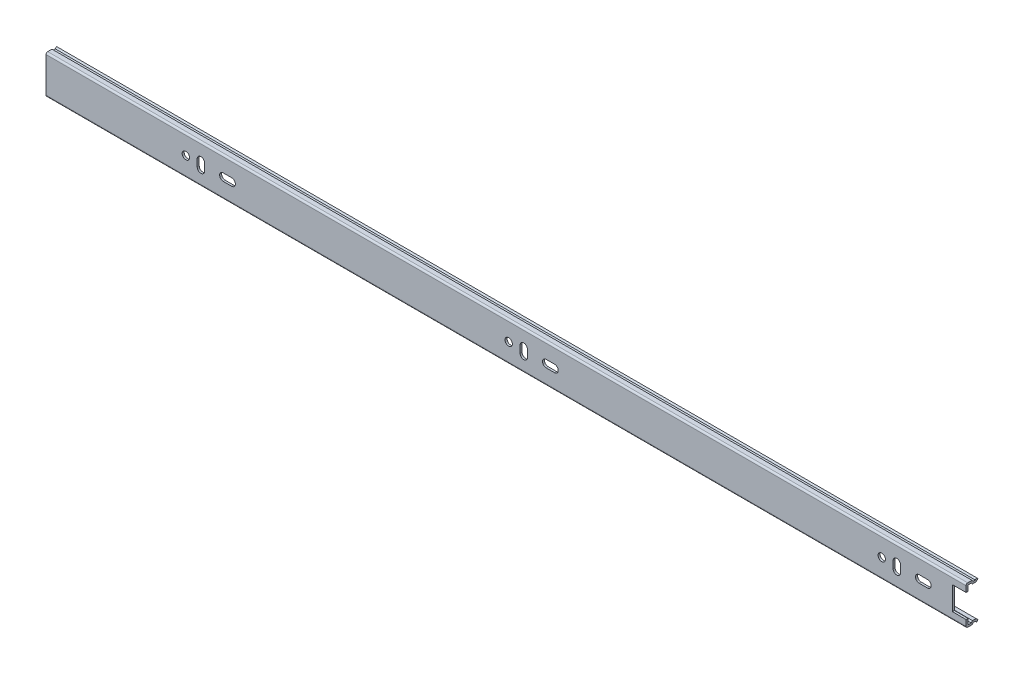
SolidWorks part; units mm, degrees
ref_plane "Спереди" through (0, 0, 0) normal (0, 0, 1) x (1, 0, 0)
ref_plane "Сверху" through (0, 0, 0) normal (0, 1, 0) x (1, 0, 0)
ref_plane "Справа" through (0, 0, 0) normal (1, 0, 0) x (0, 0, -1)
sketch "Эскиз1" plane through (0, 0, 0) normal (1, 0, 0) x (0, 0, -1)
  line L0 (0, 10.5) -> (0, -10.5)
  line L1 (-12.4481, 0) -> (26.4522, 0) construction
  line L2 (3.5733, 11.5) -> (1, 11.5)
  line L3 (4.3714, 10.7019) -> (3.5733, 11.5)
  line L4 (5.5019, 10.7019) -> (4.3714, 10.7019)
  line L5 (6.3, -11.5) -> (5.5019, -10.7019)
  line L6 (5.5019, -10.7019) -> (4.3714, -10.7019)
  line L7 (4.3714, -10.7019) -> (3.5733, -11.5)
  line L8 (3.5733, -11.5) -> (1, -11.5)
  line L9 (6.3, 11.5) -> (5.5019, 10.7019)
  arc A0 (0, 10.5) -> (1, 11.5) centre (1, 10.5) cw
  arc A2 (0, -10.5) -> (1, -11.5) centre (1, -10.5) ccw
  point P0 (0, -11.5)
  point P1 (0, 11.5)
  point P12 (0, 0)
  point P20 (0, 0)
extrude "Вытянуть-Тонкостенный3" add sketch "Эскиз1" along normal blind 550 thin
sketch "Эскиз2" plane through (0, 0, 0) normal (0, 0, 1) x (1, 0, 0)
  line L0 (550, -10.5) -> (550, 10.5) construction
  line L1 (550, 7) -> (541.8, 7)
  line L2 (550, 7) -> (550, -7)
  line L3 (550, -7) -> (541.8, -7)
  line L4 (541.8, 7) -> (541.8, -7)
  line L5 (522, 2.2) -> (527, 2.2)
  line L6 (522, -2.2) -> (527, -2.2)
  line L7 (506.4, 1.7796) -> (506.4, -2.5)
  line L8 (510.8, -2.5) -> (510.8, 1.7796)
  line L9 (283.4, 1.7796) -> (283.4, -2.5)
  line L10 (287.8, -2.5) -> (287.8, 1.7796)
  line L11 (299, -2.2) -> (304, -2.2)
  line L12 (299, 2.2) -> (304, 2.2)
  line L13 (94.8, -2.5) -> (94.8, 1.7796)
  line L14 (90.4, 1.7796) -> (90.4, -2.5)
  line L15 (106, 2.2) -> (111, 2.2)
  line L16 (106, -2.2) -> (111, -2.2)
  circle A0 centre (499.6, 0) radius 2.2
  arc A1 (522, 2.2) -> (522, -2.2) centre (522, 0) ccw
  arc A2 (527, 2.2) -> (527, -2.2) centre (527, 0) cw
  arc A3 (506.4, -2.5) -> (510.8, -2.5) centre (508.6, -2.5) ccw
  arc A4 (510.8, 1.7796) -> (506.4, 1.7796) centre (508.6, 1.7796) ccw
  arc A5 (283.4, -2.5) -> (287.8, -2.5) centre (285.6, -2.5) ccw
  circle A6 centre (276.6, 0) radius 2.2
  arc A7 (287.8, 1.7796) -> (283.4, 1.7796) centre (285.6, 1.7796) ccw
  arc A8 (299, 2.2) -> (299, -2.2) centre (299, 0) ccw
  arc A9 (304, 2.2) -> (304, -2.2) centre (304, 0) cw
  arc A10 (90.4, -2.5) -> (94.8, -2.5) centre (92.6, -2.5) ccw
  arc A11 (94.8, 1.7796) -> (90.4, 1.7796) centre (92.6, 1.7796) ccw
  circle A12 centre (83.6, 0) radius 2.2
  arc A13 (111, 2.2) -> (111, -2.2) centre (111, 0) cw
  arc A14 (106, 2.2) -> (106, -2.2) centre (106, 0) ccw
extrude "Вырез-Вытянуть1" cut sketch "Эскиз2" against normal through all
